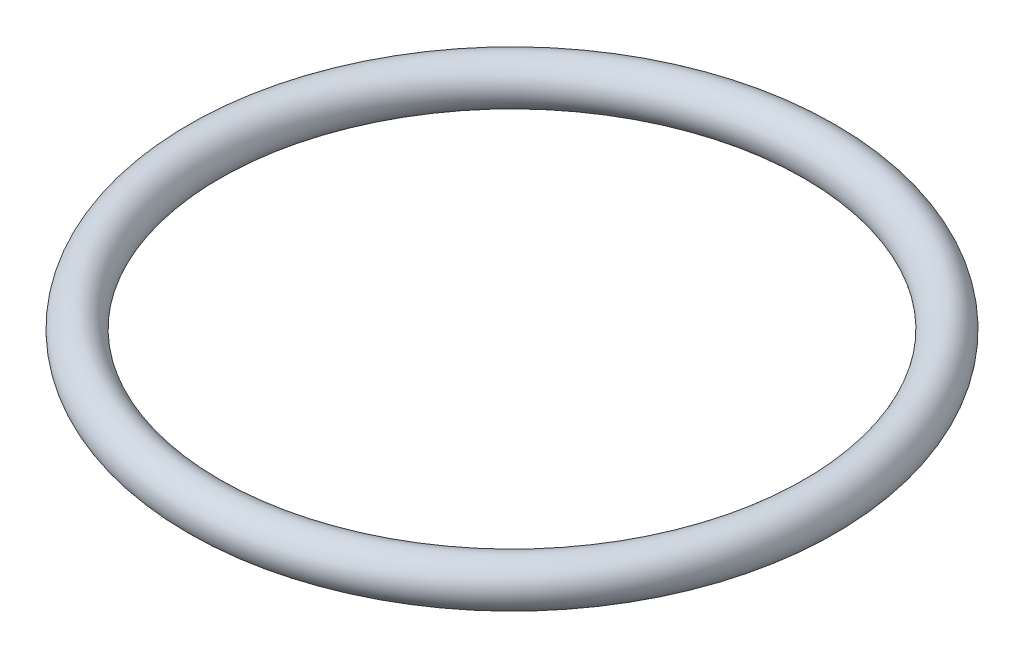
SolidWorks part; units mm, degrees
material "Copper"
ref_plane "Front Plane" through (0, 0, 0) normal (0, 0, 1) x (1, 0, 0)
ref_plane "Top Plane" through (0, 0, 0) normal (0, 1, 0) x (1, 0, 0)
ref_plane "Right Plane" through (0, 0, 0) normal (1, 0, 0) x (0, 0, -1)
sketch "Sketch1" plane through (0, 0, 0) normal (0, 1, 0) x (1, 0, 0)
  circle A0 centre (0, 0) radius 44.45
sketch "Sketch2" plane through (0, 0, 0) normal (1, 0, 0) x (0, 0, -1)
  line L0 (44.45, 0) -> (-44.45, 0) construction
  circle A0 centre (44.45, 0) radius 3.175
sweep "Sweep1" add profiles "Sketch2" path "Sketch1"
sketch "Sketch3" plane through (0, 0, 0) normal (0, 1, 0) x (1, 0, 0)
  circle A0 centre (0, 0) radius 76.4303 construction
